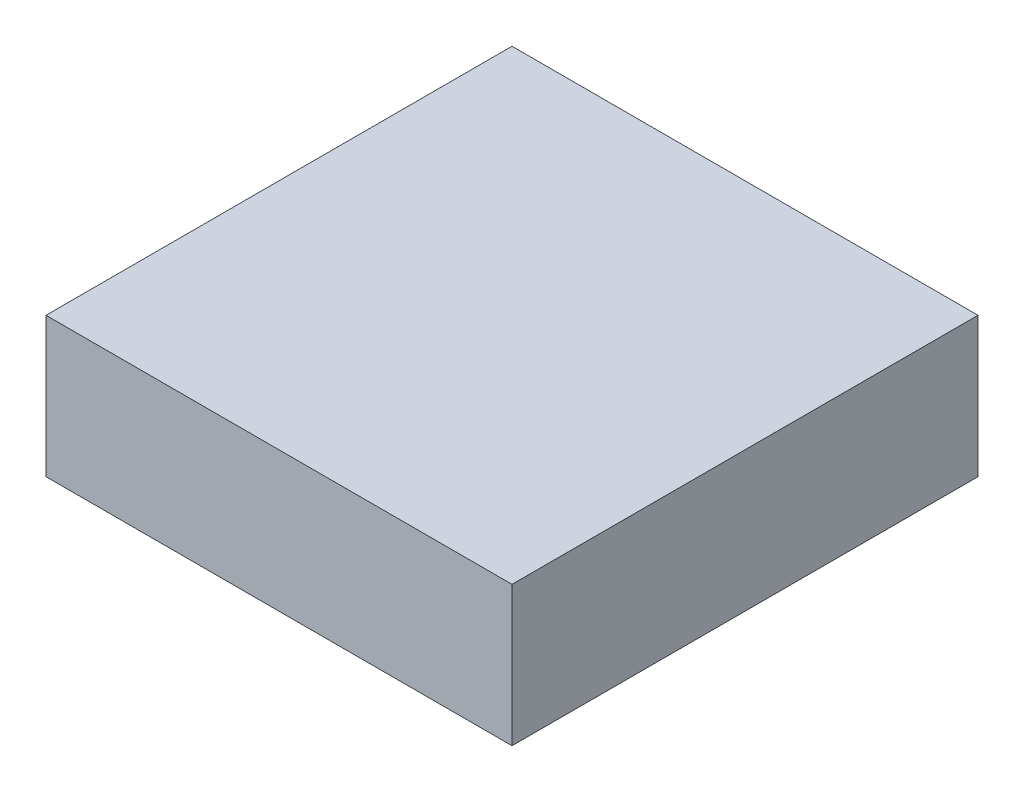
SolidWorks part; units mm, degrees
ref_plane "Front Plane" through (0, 0, 0) normal (0, 0, 1) x (1, 0, 0)
ref_plane "Top Plane" through (0, 0, 0) normal (0, 1, 0) x (1, 0, 0)
ref_plane "Right Plane" through (0, 0, 0) normal (1, 0, 0) x (0, 0, -1)
sketch "Sketch2" plane through (0, 0, 0) normal (0, 1, 0) x (1, 0, 0)
  line L1 (-127, 127) -> (127, 127)
  line L2 (-127, 127) -> (-127, -127)
  line L3 (-127, -127) -> (127, -127)
  line L4 (127, 127) -> (127, -127)
  line L5 (-127, 127) -> (127, -127) construction
  line L6 (-127, -127) -> (127, 127) construction
  point P0 (0, 0)
  dimension "D1" = 254
extrude "Boss-Extrude2" add sketch "Sketch2" along normal blind 76.2
